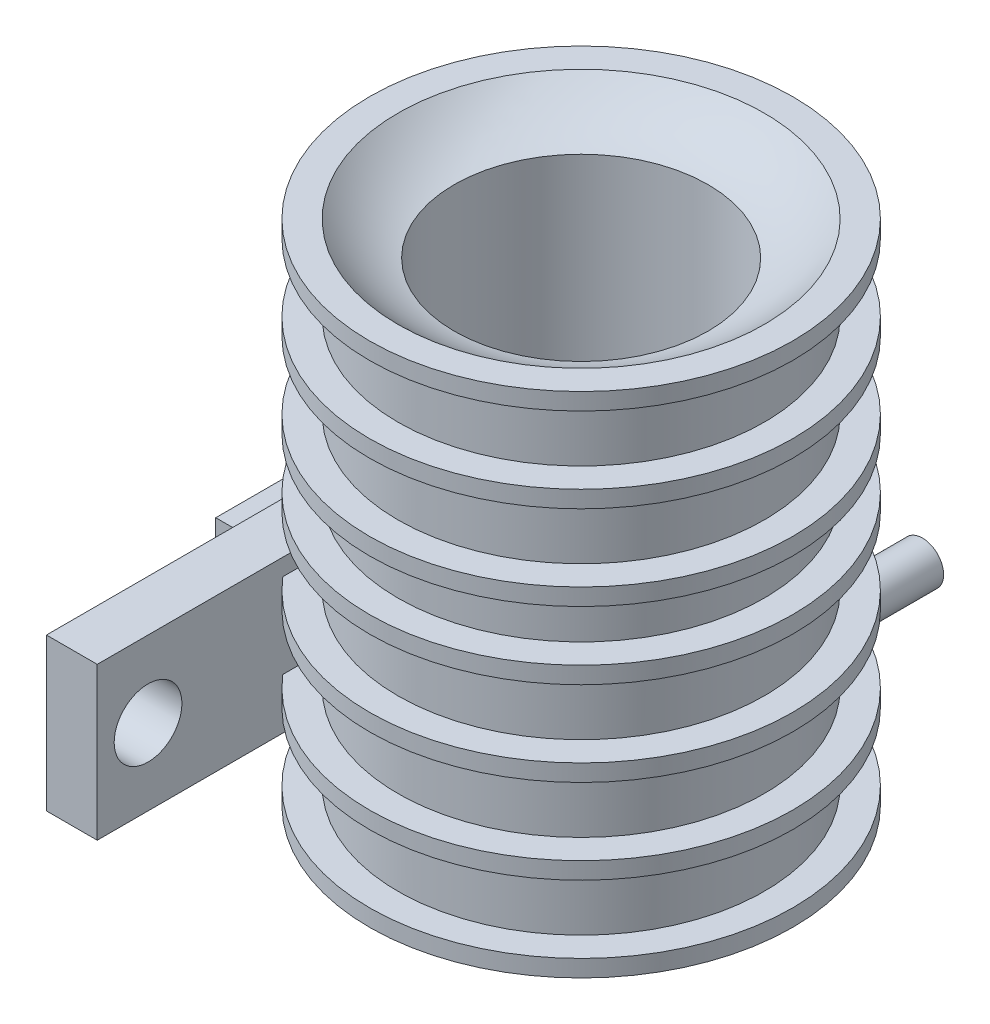
SolidWorks part; units mm, degrees
ref_plane "Alzado" through (0, 0, 0) normal (0, 0, 1) x (1, 0, 0)
ref_plane "Planta" through (0, 0, 0) normal (0, 1, 0) x (1, 0, 0)
ref_plane "Vista lateral" through (0, 0, 0) normal (1, 0, 0) x (0, 0, -1)
sketch "Croquis1" plane through (0, 0, 0) normal (0, 0, 1) x (1, 0, 0)
  line L0 (0, -2) -> (0, -30) construction
  line L1 (-10.8187, 0) -> (-12.5, 0)
  line L2 (-12.5, 0) -> (-12.5, -1)
  line L3 (-12.5, -1) -> (-10.8187, -1)
  line L4 (-10.8187, -1) -> (-10.8187, -5)
  line L5 (-10.8187, -5) -> (-12.5, -5)
  line L6 (-12.5, -5) -> (-12.5, -6)
  line L7 (-12.5, -6) -> (-10.8187, -6)
  line L8 (-10.8187, -6) -> (-10.8187, -10)
  line L9 (-10.8187, -10) -> (-12.5, -10)
  line L10 (-12.5, -10) -> (-12.5, -11)
  line L11 (-12.5, -11) -> (-10.8187, -11)
  line L12 (-10.8187, -19) -> (-10.8187, -15)
  line L13 (-10.8187, -19) -> (-12.5, -19)
  line L14 (-12.5, -19) -> (-12.5, -20)
  line L15 (-12.5, -20) -> (-10.8187, -20)
  line L16 (-10.8187, -20) -> (-10.8187, -24)
  line L17 (-10.8187, -24) -> (-12.5, -24)
  line L18 (-12.5, -24) -> (-12.5, -25)
  line L19 (-12.5, -25) -> (-10.8187, -25)
  line L20 (-10.8187, -25) -> (-10.8187, -29)
  line L21 (-10.8187, -29) -> (-12.5, -29)
  line L22 (-12.5, -29) -> (-12.5, -30)
  line L23 (-12.5, -30) -> (0, -30)
  line L24 (-10.8187, -15) -> (-12.5, -15)
  line L25 (-12.5, -15) -> (-12.5, -14)
  line L26 (-12.5, -14) -> (-10.8187, -14)
  line L27 (-10.8187, -14) -> (-10.8187, -11)
  line L28 (0, -2) -> (0, -30)
  line L30 (-7.5, -2) -> (0, -2)
  spline S0 degree 2 poles (-10.8187, 0) (-9.2588, -1.5305) (-7.5, -2) knots 0 0 0 0.398473 0.398473 0.398473
  point P29 (-7.5, 0)
  dimension "D2" = 1
  dimension "D3" = 4
  dimension "D4" = 1
  dimension "D5" = 4
  dimension "D6" = 1
  dimension "D7" = 1
  dimension "D8" = 4
  dimension "D9" = 1
  dimension "D10" = 1
  dimension "D11" = 4
  dimension "D12" = 1
  dimension "D13" = 4
revolve "Revolución1" add sketch "Croquis1" angle 360 about L0
sketch "Croquis2" plane through (0, 0, 0) normal (0, 1, 0) x (1, 0, 0)
  circle A0 centre (0, 0) radius 7.5
  dimension "D1" = 15
extrude "Cortar-Extruir1" cut sketch "Croquis2" against normal blind 24
ref_plane "Plano1" through (-12.5, 0, 0) normal (-1, 0, 0) x (0, 0, 1)
sketch "Croquis4" plane through (-12.5, 0, 0) normal (-1, 0, 0) x (0, 0, 1)
  line L2 (-8.9152, -27) -> (10.8187, -27)
  line L4 (10.8187, -29) -> (10.8187, -25) construction
  line L5 (-8.9152, -27) -> (-8.9152, -18)
  line L6 (-8.9152, -18) -> (21.0848, -18)
  line L7 (10.8187, -27) -> (21.0848, -27)
  line L8 (21.0848, -27) -> (21.0848, -18)
  dimension "D1" = 9
  dimension "D2" = 30
extrude "Saliente-Extruir1" add sketch "Croquis4" against normal blind 3
sketch "Croquis6" plane through (0, -30, 0) normal (0, -1, 0) x (1, 0, 0)
  line L0 (-12.5, -8.9152) -> (-21.5, -8.9152)
  line L1 (-21.5, -8.9152) -> (-21.5, -0.9152)
  line L2 (-21.5, -0.9152) -> (-12.5, -0.9152)
  line L4 (-12.5, -8.9152) -> (-12.5, 21.0848) construction
  line L5 (-12.5, -8.9152) -> (-5, -8.9152)
  line L6 (-5, -8.9152) -> (-5, -0.9152)
  line L7 (-5, -0.9152) -> (-12.5, -0.9152)
  dimension "D1" = 8
  dimension "D2" = 9
extrude "Saliente-Extruir2" add sketch "Croquis6" against normal blind 3
sketch "Croquis7" plane through (0, -30, 0) normal (0, -1, 0) x (1, 0, 0)
  line L0 (-21.5, -4.9152) -> (-8.1111, -4.9152) construction
  line L1 (-21.5, -0.9152) -> (-21.5, -8.9152) construction
  circle A0 centre (-18, -4.9152) radius 1.5
  point P6 (-19.5, -4.9152)
  dimension "D2" = 3
  dimension "D1" = 2
extrude "Cortar-Extruir3" cut sketch "Croquis7" against normal blind 13
sketch "Croquis8" plane through (-12.5, 0, 0) normal (-1, 0, 0) x (0, 0, 1)
  line L0 (21.0848, -22.5) -> (10.8264, -22.5) construction
  line L1 (21.0848, -27) -> (21.0848, -18) construction
  circle A0 centre (17.5848, -22.5) radius 1.5
  point P6 (19.0848, -22.5)
  dimension "D2" = 3
  dimension "D1" = 2
extrude "Cortar-Extruir4" cut sketch "Croquis8" against normal blind 13
ref_plane "Plano2" through (0, 0, -19.5) normal (0, 0, 1) x (1, 0, 0)
sketch "Croquis9" plane through (0, 0, -19.5) normal (0, 0, 1) x (1, 0, 0)
  line L0 (0.6593, -25) -> (0.6593, -29)
  line L2 (-9.5, -25) -> (10.8187, -25) construction
  line L5 (12.5, -29) -> (-12.5, -29) construction
  circle A0 centre (0.6593, -27) radius 2.5
  dimension "D1" = 5
extrude "Saliente-Extruir3" add sketch "Croquis9" along normal blind 13 contours L0 A0 | L0 A0
sketch "Croquis10" plane through (0, 0, -19.5) normal (0, 0, -1) x (-1, 0, 0)
  circle A0 centre (-0.6593, -27) radius 1.1043
  dimension "D1" = 2.2086
extrude "Cortar-Extruir5" cut sketch "Croquis10" against normal blind 13
ref_plane "Plano3" through (0, 0, -12.5) normal (0, 0, 1) x (1, 0, 0)
sketch "Croquis13" plane through (0, 0, -19.5) normal (0, 0, -1) x (-1, 0, 0)
  circle A0 centre (-0.6593, -27) radius 1.25
  circle A1 centre (-0.6593, -27) radius 2.5
  dimension "D1" = 2.5
extrude "Cortar-Extruir6" cut sketch "Croquis13" against normal blind 5.5
sketch "Croquis15" plane through (0, -27, 0) normal (0, 1, 0) x (1, 0, 0)
  line L0 (-12.5, 8.9152) -> (-22.5, 8.9152)
  line L1 (-22.5, 8.9152) -> (-22.5, 0.9152)
  line L2 (-22.5, 0.9152) -> (-12.5, 0.9152)
  line L3 (-12.5, 0.9152) -> (-12.5, 8.9152)
  dimension "D1" = 10
extrude "Saliente-Extruir4" add sketch "Croquis15" against normal blind 3
sketch "Croquis16" plane through (0, -27, 0) normal (0, 1, 0) x (1, 0, 0)
  line L0 (-22.5, 4.9152) -> (-12.5, 4.9152) construction
  line L1 (-22.5, 8.9152) -> (-22.5, 0.9152) construction
  line L2 (-12.5, 8.9152) -> (-12.5, 0.9152) construction
  circle A0 centre (-17.5, 4.9152) radius 1.5
  dimension "D1" = 3
extrude "Cortar-Extruir7" cut sketch "Croquis16" against normal blind 30
sketch "Croquis17" plane through (-12.5, 0, 0) normal (-1, 0, 0) x (0, 0, 1)
  line L0 (-8.9152, -18) -> (19.0848, -18)
  line L1 (21.0848, -18) -> (-8.9152, -18) construction
  line L2 (19.0848, -18) -> (19.0848, -27)
  line L3 (-0.9152, -27) -> (21.0848, -27) construction
  line L4 (19.0848, -27) -> (-8.9152, -27)
  line L5 (-8.9152, -27) -> (-8.9152, -18)
  line L6 (19.0848, -18) -> (21.0848, -18)
  line L7 (21.0848, -18) -> (21.0848, -27)
  line L8 (21.0848, -27) -> (19.0848, -27)
  circle M2 centre (17.5848, -22.5) radius 1.5
  line M3 (-8.9152, -27) -> (-0.9152, -27)
  line M4 (-0.9152, -27) -> (21.0848, -27)
  line M6 (21.0848, -18) -> (-8.9152, -18)
  line M7 (-8.9152, -18) -> (-8.9152, -27)
  dimension "D1" = 28
extrude "Saliente-Extruir5" add sketch "Croquis17" against normal blind 3 contours M2 | L2 M6 M7 M3 M4 M2
sketch "Croquis18" plane through (-12.5, 0, 0) normal (-1, 0, 0) x (0, 0, 1)
  line L0 (-8.9152, -18) -> (19.0848, -18)
  line L1 (21.0848, -18) -> (-8.9152, -18) construction
  line L2 (19.0848, -18) -> (19.0848, -27)
  line L3 (-0.9152, -27) -> (21.0848, -27) construction
  line L4 (19.0848, -27) -> (21.0848, -27)
  line L5 (21.0848, -27) -> (21.0848, -18)
  line L6 (21.0848, -18) -> (19.0848, -18)
  line M2 (21.0848, -18) -> (-8.9152, -18)
  line M5 (-0.9152, -27) -> (21.0848, -27)
  line M6 (21.0848, -27) -> (21.0848, -18)
  dimension "D1" = 28
extrude "Cortar-Extruir11" cut sketch "Croquis18" against normal blind 3 contours L2 M2 M5 M6
sketch "Croquis19" plane through (-12.5, 0, 0) normal (-1, 0, 0) x (0, 0, 1)
  line L0 (19.0848, -22.5) -> (18.0848, -22.5)
  line L1 (19.0848, -18) -> (19.0848, -27) construction
  circle A0 centre (16.0848, -22.5) radius 2
  dimension "D2" = 4
  dimension "D1" = 1
extrude "Cortar-Extruir12" cut sketch "Croquis19" against normal blind 33 contours A0
